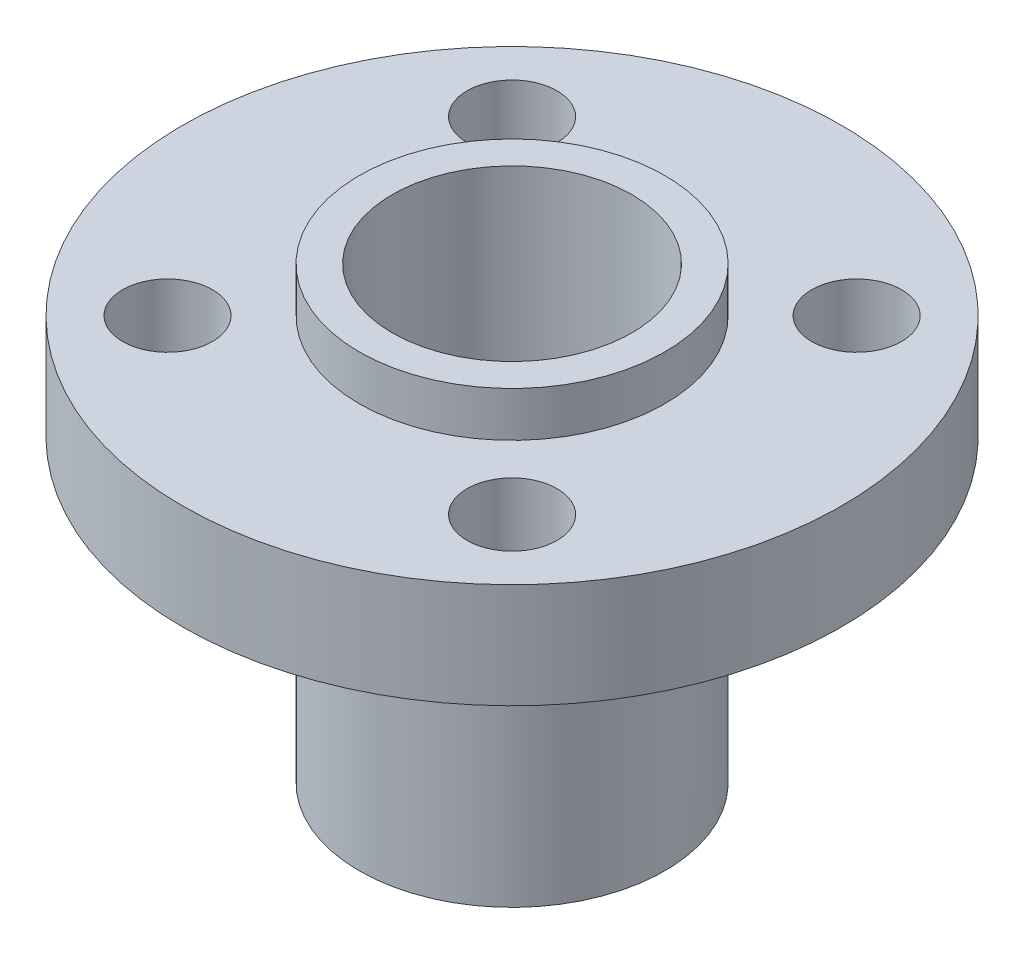
SolidWorks part; units mm, degrees
ref_plane "Front Plane" through (0, 0, 0) normal (0, 0, 1) x (1, 0, 0)
ref_plane "Top Plane" through (0, 0, 0) normal (0, 1, 0) x (1, 0, 0)
ref_plane "Right Plane" through (0, 0, 0) normal (1, 0, 0) x (0, 0, -1)
sketch "Sketch1" plane through (0, 0, 0) normal (0, 1, 0) x (1, 0, 0)
  circle A0 centre (0, 0) radius 11
  circle A1 centre (0, 0) radius 4
  dimension "D1" = 22
  dimension "D2" = 8
extrude "Boss-Extrude1" add sketch "Sketch1" along normal blind 3.5
sketch "Sketch2" plane through (0, 3.5, 0) normal (0, 1, 0) x (1, 0, 0)
  circle A0 centre (0, 0) radius 5.1
  circle A1 centre (0, 0) radius 4 construction
  circle A2 centre (0, 0) radius 4
  dimension "D1" = 10.2
extrude "Boss-Extrude2" add sketch "Sketch2" along normal blind 1.5
sketch "Sketch3" plane through (0, 0, 0) normal (0, -1, 0) x (1, 0, 0)
  circle A0 centre (0, 0) radius 4 construction
  circle A1 centre (0, 0) radius 5.1
  circle A2 centre (0, 0) radius 5.1
  circle A3 centre (0, 0) radius 4
  dimension "D1" = 0
extrude "Boss-Extrude3" add sketch "Sketch3" along normal blind 10
sketch "Sketch4" plane through (0, 3.5, 0) normal (0, 1, 0) x (1, 0, 0)
  line L1 (-5.75, -5.75) -> (5.75, -5.75) construction
  line L2 (-5.75, -5.75) -> (-5.75, 5.75) construction
  line L3 (-5.75, 5.75) -> (5.75, 5.75) construction
  line L4 (5.75, -5.75) -> (5.75, 5.75) construction
  line L5 (-5.75, -5.75) -> (5.75, 5.75) construction
  line L6 (-5.75, 5.75) -> (5.75, -5.75) construction
  circle A0 centre (-5.75, 5.75) radius 1.5
  circle A1 centre (5.75, 5.75) radius 1.5
  circle A2 centre (5.75, -5.75) radius 1.5
  circle A3 centre (-5.75, -5.75) radius 1.5
  point P0 (0, 0)
  dimension "D3" = 3
  dimension "D4" = 3
  dimension "D5" = 3
  dimension "D6" = 3
  dimension "D1" = 11.5
  dimension "D2" = 11.5
extrude "Cut-Extrude1" cut sketch "Sketch4" against normal up to next
